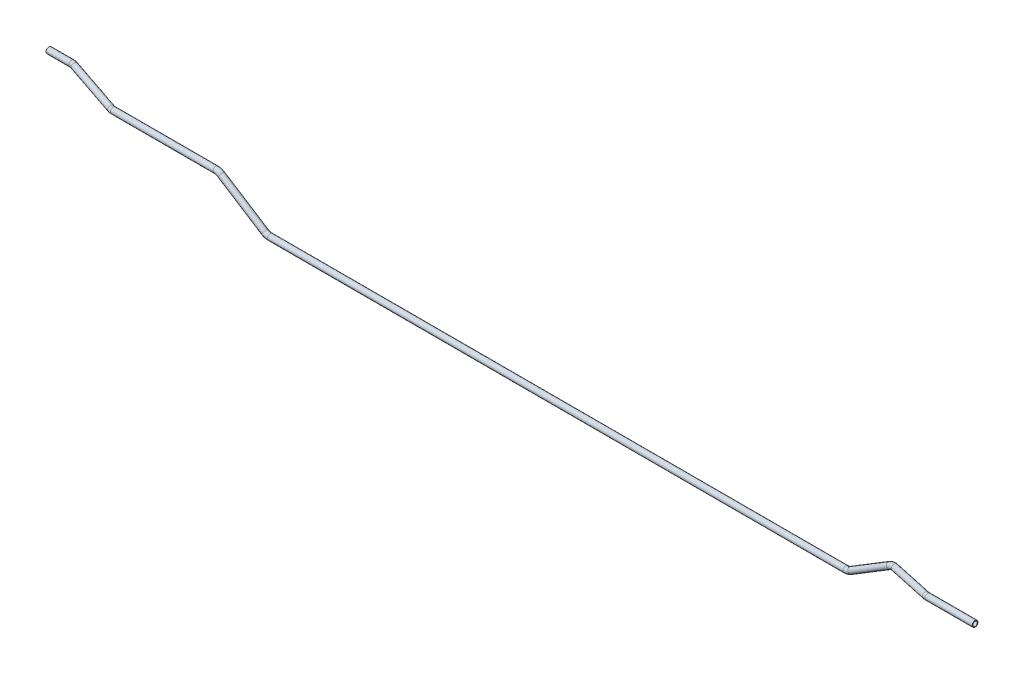
SolidWorks part; units mm, degrees
ref_plane "Plane1" through (0, 0, 0) normal (0, 0, 1) x (1, 0, 0)
ref_plane "Plane2" through (0, 0, 0) normal (0, 1, 0) x (1, 0, 0)
ref_plane "Plane3" through (0, 0, 0) normal (1, 0, 0) x (0, 0, -1)
sketch3d "3DSketch1"
  line L0 (0, 0, 0) -> (47.0165, 0, 0)
  line L1 (50, 0, 0) -> (50, -21, 0) construction
  line L2 (50, -21, 0) -> (50, -21, 20) construction
  line L3 (50, -21, 20) -> (150, -21, 20) construction
  line L4 (147.1345, -20.3983, 19.4269) -> (52.8655, -0.6017, 0.5731)
  line L5 (152.9835, -21, 20) -> (363.8553, -21, 20)
  line L6 (370, -21, 20) -> (370, -85, 20) construction
  line L7 (370, -85, 20) -> (470, -85, 20) construction
  line L8 (375.1755, -24.3123, 20) -> (464.8245, -81.6877, 20)
  line L9 (476.1447, -85, 20) -> (1662.0913, -85, 20)
  line L10 (1668, -85, 20) -> (1668, -30, 20) construction
  line L11 (1668, -30, 20) -> (1758, -30, 20) construction
  line L12 (1758, -30, 20) -> (1758, -30, 39.5) construction
  line L13 (1673.0418, -81.9189, 20) -> (1752.6078, -33.2952, 20)
  line L14 (1758, -30, 39.5) -> (1848, -30, 39.5) construction
  line L15 (1764.176, -30, 21.3381) -> (1845.8021, -30, 39.0238)
  line L16 (1850.2489, -30, 39.5) -> (1948, -30, 39.5)
  arc A0 (47.0165, 0, 0) -> (52.8655, -0.6017, 0.5731) centre (47.0165, -15.2069, 14.4828) ccw
  arc A1 (152.9835, -21, 20) -> (147.1345, -20.3983, 19.4269) centre (152.9835, -5.7931, 5.5172) ccw
  arc A2 (1850.2489, -30, 39.5) -> (1845.8021, -30, 39.0238) centre (1850.2489, -30, 18.5) ccw
  arc A3 (1764.176, -30, 21.3381) -> (1752.6078, -33.2952, 20) centre (1762.7201, -49.8425, 28.0578) ccw
  arc A4 (1662.0913, -85, 20) -> (1673.0418, -81.9189, 20) centre (1662.0913, -64, 20) ccw
  arc A5 (476.1447, -85, 20) -> (464.8245, -81.6877, 20) centre (476.1447, -64, 20) ccw
  arc A6 (363.8553, -21, 20) -> (375.1755, -24.3123, 20) centre (363.8553, -42, 20) ccw
  point P9 (50, 0, 0)
  point P11 (47.0165, -29.6897, -0.7241)
  point P14 (150, -21, 20)
  point P16 (152.9835, -20.2759, -9.6897)
  point P27 (1848, -30, 39.5)
  point P29 (1850.2489, -51, 18.5)
  point P32 (1758, -30, 20)
  point P34 (1758.5184, -42.967, 47.4504)
  point P37 (1668, -85, 20)
  point P39 (1662.0913, -64, 41)
  point P42 (470, -85, 20)
  point P44 (476.1447, -64, -1)
  point P47 (370, -21, 20)
  point P49 (363.8553, -42, -1)
  dimension "D6" = 21
  dimension "D7" = 21
  dimension "D16" = 21
  dimension "D1" = 21
  dimension "D2" = 20
  dimension "D3" = 100
  dimension "D4" = 50
  dimension "D5" = 220
  dimension "D8" = 64
  dimension "D9" = 100
  dimension "D10" = 1198
  dimension "D11" = 55
  dimension "D12" = 90
  dimension "D13" = 19.5
  dimension "D15" = 100
  dimension "D14" = 90
ref_plane "Plane4" through (0, 0, 0) normal (1, 0, 0) x (0, 0, -1)
sketch "Sketch1" plane through (0, 0, 0) normal (1, 0, 0) x (0, 0, -1)
  circle A0 centre (0, 0) radius 6
  circle A1 centre (0, 0) radius 4.5
  dimension "D1" = 12
  dimension "D2" = 9
sweep "Sweep1" add profiles "Sketch1" path "3DSketch1"
